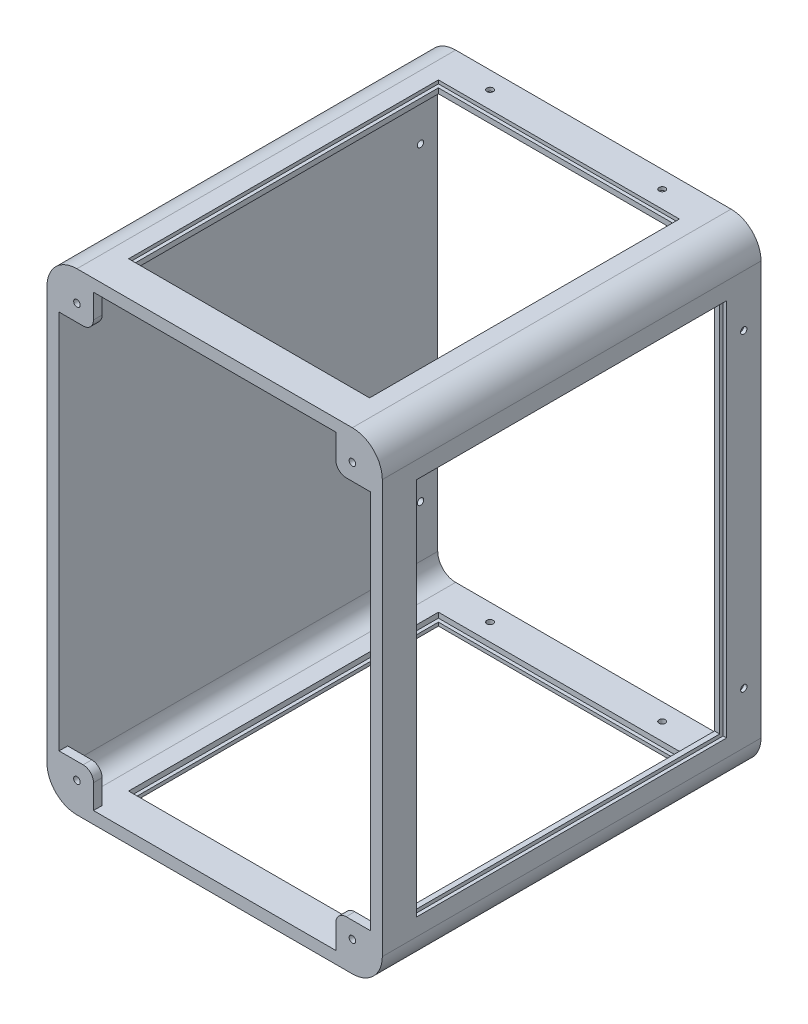
SolidWorks part; units mm, degrees
ref_plane "Front Plane" through (0, 0, 0) normal (0, 0, 1) x (1, 0, 0)
ref_plane "Top Plane" through (0, 0, 0) normal (0, 1, 0) x (1, 0, 0)
ref_plane "Right Plane" through (0, 0, 0) normal (1, 0, 0) x (0, 0, -1)
sketch "Sketch1" plane through (0, 0, 0) normal (0, 0, 1) x (1, 0, 0)
  line L4 (45, -60) -> (45, 60)
  line L5 (40, 65) -> (-40, 65)
  line L6 (-45, 60) -> (-45, -60)
  line L7 (-40, -65) -> (40, -65)
  line L8 (45, -60) -> (45, 60)
  line L9 (40, 65) -> (-40, 65)
  line L10 (-45, 60) -> (-45, -60)
  line L11 (-40, -65) -> (40, -65)
  arc A4 (45, 60) -> (40, 65) centre (40, 60) ccw
  arc A5 (-40, 65) -> (-45, 60) centre (-40, 60) ccw
  arc A6 (-45, -60) -> (-40, -65) centre (-40, -60) ccw
  arc A7 (40, -65) -> (45, -60) centre (40, -60) ccw
  arc A8 (45, 60) -> (40, 65) centre (40, 60) ccw
  arc A9 (-40, 65) -> (-45, 60) centre (-40, 60) ccw
  arc A10 (-45, -60) -> (-40, -65) centre (-40, -60) ccw
  arc A11 (40, -65) -> (45, -60) centre (40, -60) ccw
  dimension "D1" = 0
ref_plane "Plane2" through (40, 65, 0) normal (-1, 0, 0) x (0, 0, 1)
sketch "Sketch3" plane through (40, 65, 0) normal (-1, 0, 0) x (0, 0, 1)
  line L0 (0, 0) -> (-3, 0) construction
  line L1 (-107.5, 3.7) -> (2.5, 3.7)
  line L2 (-107.5, 3.7) -> (-107.5, 0.2)
  line L3 (-107.5, 0.2) -> (2.5, 0.2)
  line L4 (2.5, 3.7) -> (2.5, 0.2)
  line L5 (0, -5) -> (0, 0) construction
  dimension "D1" = 3.5
  dimension "D2" = 110
  dimension "D3" = 0.2
  dimension "D4" = 2.5
sweep "Sweep1" add profiles "Sketch3" path "Sketch1"
sketch "Sketch4" plane through (0, 0, 2.5) normal (0, 0, 1) x (1, 0, 0)
  line L0 (40, -65.2) -> (35.2, -65.2)
  line L1 (40, -65.2) -> (-40, -65.2) construction
  line L2 (35.2, -65.2) -> (35.2, -58.2)
  line L3 (38.2, -55.2) -> (45.2, -55.2)
  line L4 (45.2, 60) -> (45.2, -60) construction
  line L5 (45.2, -55.2) -> (45.2, -60)
  arc A0 (40, -65.2) -> (45.2, -60) centre (40, -60) ccw construction
  arc A1 (40, -65.2) -> (45.2, -60) centre (40, -60) ccw
  circle A2 centre (40, -60) radius 0.95 construction
  circle A3 centre (40, -60) radius 0.95
  arc A4 (35.2, -58.2) -> (38.2, -55.2) centre (38.2, -58.2) cw
  arc A5 (38.2, -55.2) -> (35.2, -58.2) centre (38.2, -58.2) ccw
  line M5 (40, -65.2) -> (-40, -65.2)
  dimension "D1" = 3
  dimension "D2" = 3
  dimension "D3" = 10
extrude "Boss-Extrude2" add sketch "Sketch4" against normal up to surface (2.5 mm away) contours A4 L2 A1 L5 L3 A3 M5
mirror "Mirror3" about plane through (0, 0, 0) normal (1, 0, 0) of "Boss-Extrude2"
mirror "Mirror4" about plane through (0, 0, 0) normal (0, 1, 0) of "Mirror3", "Boss-Extrude2"
sketch "Sketch5" plane through (48.7, 0, 0) normal (1, 0, 0) x (0, 0, -1)
  line L0 (107.5, 60) -> (-2.5, -60) construction
  line L1 (107.5, 60) -> (107.5, -60) construction
  line L2 (7.5, 55) -> (97.5, 55)
  line L3 (7.5, 55) -> (7.5, -55)
  line L4 (7.5, -55) -> (97.5, -55)
  line L5 (97.5, 55) -> (97.5, -55)
  line L6 (7.5, 55) -> (97.5, -55) construction
  line L7 (7.5, -55) -> (97.5, 55) construction
  line L8 (-2.5, 60) -> (107.5, 60) construction
  point P2 (52.5, 0)
  dimension "D1" = 10
  dimension "D2" = 5
extrude "Cut-Extrude1" cut sketch "Sketch5" against normal up to next
sketch "Sketch6" plane through (0, 68.7, 0) normal (0, 1, 0) x (1, 0, 0)
  line L0 (-40, 107.5) -> (40, -2.5) construction
  line L1 (-40, 107.5) -> (40, 107.5) construction
  line L2 (-35, 7.5) -> (35, 7.5)
  line L3 (-35, 7.5) -> (-35, 97.5)
  line L4 (-35, 97.5) -> (35, 97.5)
  line L5 (35, 7.5) -> (35, 97.5)
  line L6 (-35, 7.5) -> (35, 97.5) construction
  line L7 (-35, 97.5) -> (35, 7.5) construction
  line L8 (-40, -2.5) -> (-40, 107.5) construction
  point P4 (0, 52.5)
  dimension "D1" = 10
  dimension "D2" = 5
extrude "Cut-Extrude2" cut sketch "Sketch6" against normal through all
sketch "Sketch7" plane through (48.7, 0, 0) normal (1, 0, 0) x (0, 0, -1)
  line L0 (107.5, 0) -> (102.5, 0) construction
  line L1 (107.5, 60) -> (107.5, -60) construction
  line L2 (102.5, 0) -> (102.5, 45) construction
  circle A0 centre (102.5, 45) radius 0.925
  circle A1 centre (102.5, -45) radius 0.925
  dimension "D2" = 1.85
  dimension "D1" = 5
  dimension "D3" = 90
extrude "Cut-Extrude3" cut sketch "Sketch7" against normal through all
sketch "Sketch9" plane through (0, 68.7, 0) normal (0, 1, 0) x (1, 0, 0)
  line L0 (0, 107.5) -> (0, 0) construction
  line L1 (-40, 107.5) -> (40, 107.5) construction
  circle A0 centre (-25, 102.5) radius 0.925
  circle A1 centre (25, 102.5) radius 0.925
  dimension "D1" = 1.85
  dimension "D2" = 50
  dimension "D3" = 5
extrude "Cut-Extrude5" cut sketch "Sketch9" against normal through all
sketch "Sketch8" plane through (0, 0, -107.5) normal (0, 0, -1) x (-1, 0, 0)
  line L0 (40, 68.7) -> (40, 65.2) construction
  line L1 (-38, 67.7) -> (38, 67.7)
  line L2 (-38, 67.7) -> (-38, 66.7)
  line L3 (-38, 66.7) -> (38, 66.7)
  line L4 (38, 67.7) -> (38, 66.7)
  line L5 (0, 0) -> (0, 66.7) construction
  line L6 (40, 65.2) -> (-40, 65.2) construction
  line L7 (-45.2, 60) -> (-45.2, -60) construction
  line L9 (0, 0) -> (-47.2, 0) construction
  line L10 (-47.7, -58) -> (-46.7, -58)
  line L11 (-47.7, -58) -> (-47.7, 58)
  line L12 (-47.7, 58) -> (-46.7, 58)
  line L13 (-46.7, -58) -> (-46.7, 58)
  line L14 (-47.7, -58) -> (-46.7, 58) construction
  line L15 (-47.7, 58) -> (-46.7, -58) construction
  line L17 (-48.7, 60) -> (-45.2, 60) construction
  line L18 (38, -67.7) -> (38, -66.7)
  line L19 (-38, -66.7) -> (38, -66.7)
  line L20 (-38, -67.7) -> (-38, -66.7)
  line L21 (-38, -67.7) -> (38, -67.7)
  point P15 (-47.2, 0)
  dimension "D1" = 2
  dimension "D2" = 1.5
  dimension "D3" = 1
  dimension "D4" = 1
  dimension "D5" = 1.5
  dimension "D6" = 2
extrude "Cut-Extrude4" cut sketch "Sketch8" against normal offset from surface (103 mm away) 3 up to face at (46.95, 0, -7.5) offset beyond the face yes
